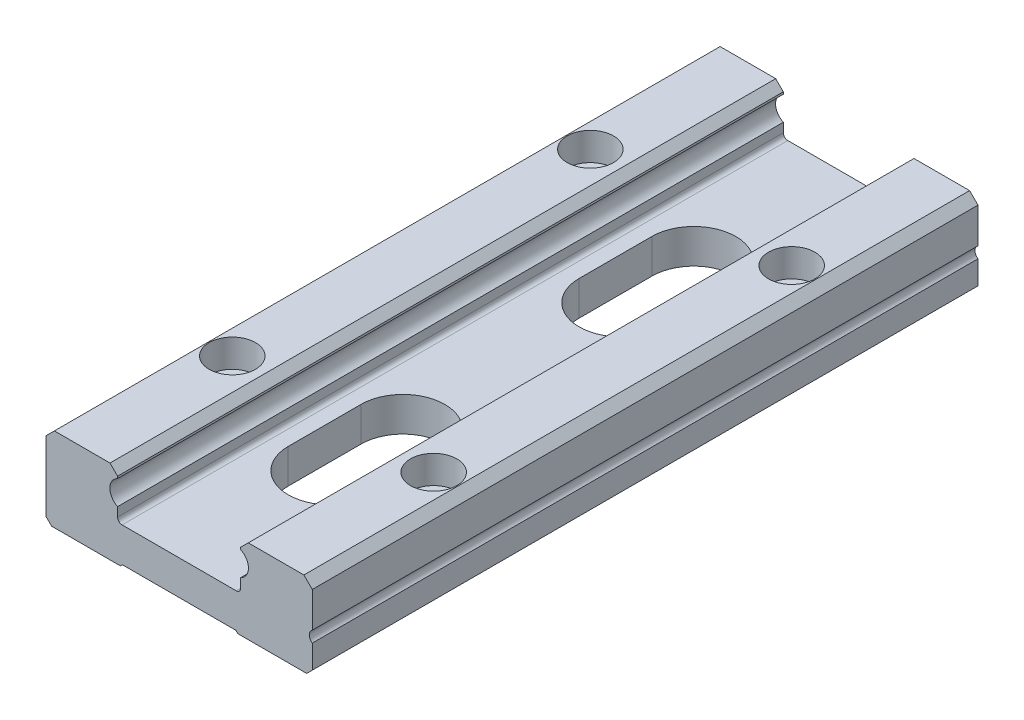
SolidWorks part; units mm, degrees
ref_plane "前视基准面" through (0, 0, 0) normal (0, 0, 1) x (1, 0, 0)
ref_plane "上视基准面" through (0, 0, 0) normal (0, 1, 0) x (1, 0, 0)
ref_plane "右视基准面" through (0, 0, 0) normal (1, 0, 0) x (0, 0, -1)
other "Configuration Table"
sketch "草图1" plane through (0, 0, 0) normal (0, 0, 1) x (1, 0, 0)
  line L0 (123.4256, 684.043) -> (122.0671, 682.6844)
  line L1 (133.3671, 684.043) -> (134.0464, 683.3637)
  line L2 (123.6671, 684.043) -> (133.3671, 684.043)
  line L3 (123.4256, 684.043) -> (123.6671, 684.043)
  line L4 (100.0671, 682.6844) -> (98.7085, 684.043)
  line L5 (88.7671, 684.043) -> (98.7085, 684.043)
  line L6 (88.0878, 683.3637) -> (88.7671, 684.043)
  line L7 (88.2671, 669.043) -> (87.7671, 669.543)
  line L8 (100.5671, 669.043) -> (88.2671, 669.043)
  line L9 (100.9171, 669.393) -> (100.5671, 669.043)
  line L10 (121.2171, 669.393) -> (100.9171, 669.393)
  line L11 (121.5671, 669.043) -> (121.2171, 669.393)
  line L12 (133.8671, 669.043) -> (121.5671, 669.043)
  line L13 (134.3671, 669.543) -> (133.8671, 669.043)
  line L14 (134.0464, 683.3637) -> (134.8671, 682.543)
  line L15 (134.0464, 683.3637) -> (133.3671, 682.6844)
  line L16 (134.3671, 669.543) -> (133.3671, 670.543)
  line L17 (134.8671, 670.043) -> (134.3671, 669.543)
  line L18 (134.8671, 674.243) -> (134.8671, 670.043)
  line L19 (134.8671, 682.543) -> (134.8671, 676.243)
  line L20 (88.7671, 682.6844) -> (88.0878, 683.3637)
  line L21 (87.2671, 682.543) -> (88.0878, 683.3637)
  line L22 (87.2671, 670.043) -> (87.2671, 682.543)
  line L23 (87.7671, 669.543) -> (87.2671, 670.043)
  line L24 (87.7671, 669.543) -> (88.7671, 670.543)
  line L25 (100.0671, 682.3082) -> (100.0671, 682.6844)
  line L26 (100.0671, 682.6844) -> (88.7671, 682.6844)
  line L27 (88.7671, 682.6844) -> (88.7671, 670.543)
  line L28 (88.7671, 670.543) -> (133.3671, 670.543)
  line L29 (133.3671, 670.543) -> (133.3671, 682.6844)
  line L30 (133.3671, 682.6844) -> (122.0671, 682.6844)
  line L31 (122.0671, 682.6844) -> (122.0671, 682.3082)
  line L32 (122.0671, 677.9778) -> (122.0671, 676.343)
  line L33 (121.2671, 675.543) -> (100.8671, 675.543)
  line L34 (100.0671, 676.343) -> (100.0671, 677.9778)
  arc A0 (134.8671, 676.243) -> (134.8671, 674.243) centre (135.5304, 675.243) ccw
  arc A1 (100.0671, 676.343) -> (100.8671, 675.543) centre (100.8671, 676.343) ccw
  arc A2 (122.0671, 677.9778) -> (122.0671, 682.3082) centre (121.0671, 680.143) ccw
  arc A3 (121.2671, 675.543) -> (122.0671, 676.343) centre (121.2671, 676.343) ccw
  arc A4 (100.0671, 682.3082) -> (100.0671, 677.9778) centre (101.0671, 680.143) ccw
extrude "凸台-拉伸1" add sketch "草图1" along normal blind 119 contours L26 L4 L5 L6 L20 | L27 L20 L21 L22 L23 L24 | A4 L25 L26 L27 L28 L29 L30 L31 A2 L32 A3 L33 A1 L34 | L28 L24 L7 L8 L9 L10 L11 L12 L13 L16 | L30 L15 L1 L2 L3 L0 | A0 L19 L14 L15 L29 L16 L17 L18
sketch "草图4" plane through (0, 684.043, 0) normal (0, 1, 0) x (1, 0, 0)
  line L0 (88.7671, 0) -> (98.7085, 0) construction
  line L3 (87.2671, -119) -> (87.2671, 0) construction
  line L4 (123.4256, 0) -> (133.3671, 0) construction
  line L5 (134.8671, -119) -> (134.8671, 0) construction
  line L6 (88.7671, -119) -> (98.7085, -119) construction
  line L8 (123.4256, -119) -> (133.3671, -119) construction
  circle A4 centre (93.0671, -27.5) radius 4.145
  circle A5 centre (129.0671, -27.5) radius 4.145
  circle A6 centre (93.0671, -91.5) radius 4.145
  circle A7 centre (129.0671, -91.5) radius 4.145
  dimension "D1" = 27.5
  dimension "D4" = 8.29
  dimension "D8" = 8.29
  dimension "D14" = 8.29
  dimension "D16" = 8.29
  dimension "D2" = 5.8
  dimension "D5" = 27.5
  dimension "D6" = 5.8
  dimension "D9" = 27.5
  dimension "D10" = 27.5
  dimension "D11" = 5.8
  dimension "D12" = 5.8
extrude "切除-拉伸2" cut sketch "草图4" against normal blind 5
sketch "草图7" plane through (0, 679.043, 0) normal (0, 1, 0) x (1, 0, 0)
  circle A1 centre (93.0671, -27.5) radius 2.8
  circle A2 centre (93.0671, -91.5) radius 2.8
  circle A3 centre (129.0671, -91.5) radius 2.8
  circle A4 centre (129.0671, -27.5) radius 2.8
  dimension "D1" = 5.6
  dimension "D2" = 5.6
  dimension "D3" = 5.6
  dimension "D4" = 5.6
extrude "切除-拉伸3" cut sketch "草图7" against normal blind 10
sketch "草图8" plane through (0, 675.543, 0) normal (0, 1, 0) x (1, 0, 0)
  line L0 (121.2671, 0) -> (100.8671, 0) construction
  line L1 (87.2671, -119) -> (87.2671, 0) construction
  line L2 (103.5671, -27) -> (103.5671, -40)
  line L3 (118.5671, -27) -> (118.5671, -40)
  line L4 (103.5671, -79) -> (103.5671, -92)
  line L5 (118.5671, -79) -> (118.5671, -92)
  line L6 (121.2671, -119) -> (100.8671, -119) construction
  arc A0 (118.5671, -27) -> (103.5671, -27) centre (111.0671, -27) ccw
  arc A1 (103.5671, -40) -> (118.5671, -40) centre (111.0671, -40) ccw
  arc A4 (118.5671, -79) -> (103.5671, -79) centre (111.0671, -79) ccw
  arc A5 (103.5671, -92) -> (118.5671, -92) centre (111.0671, -92) ccw
  dimension "D1" = 27
  dimension "D3" = 15
  dimension "D4" = 15
  dimension "D2" = 13
  dimension "D5" = 23.8
  dimension "D6" = 23.8
  dimension "D7" = 27
  dimension "D8" = 23.8
  dimension "D9" = 23.8
extrude "切除-拉伸4" cut sketch "草图8" against normal blind 10
